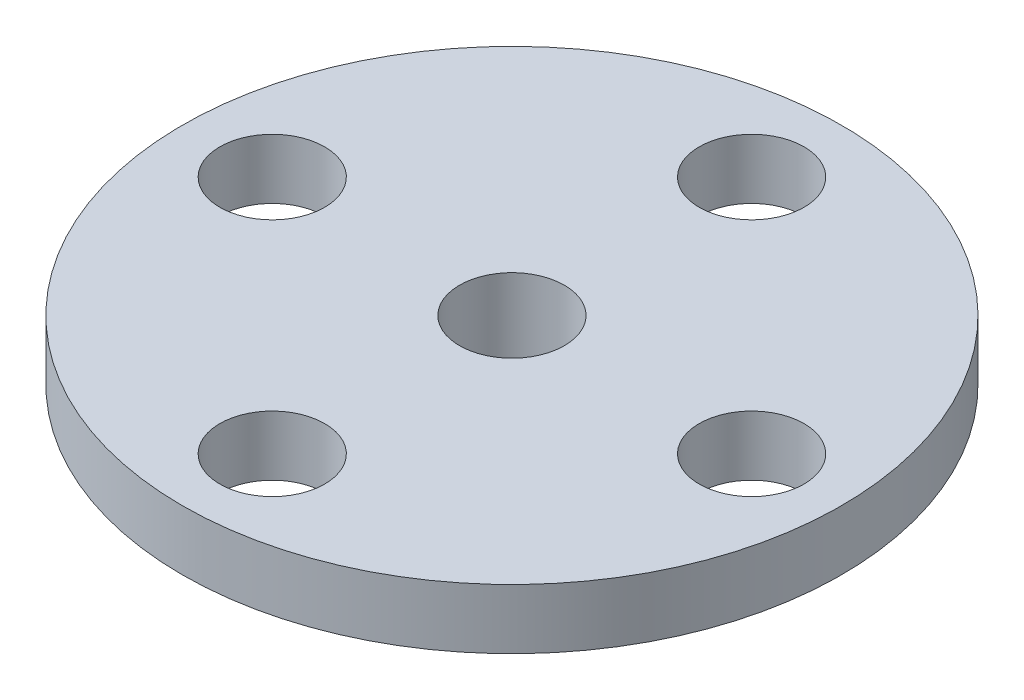
SolidWorks part; units mm, degrees
material "2024 Alloy"
ref_plane "Front Plane" through (0, 0, 0) normal (0, 0, 1) x (1, 0, 0)
ref_plane "Top Plane" through (0, 0, 0) normal (0, 1, 0) x (1, 0, 0)
ref_plane "Right Plane" through (0, 0, 0) normal (1, 0, 0) x (0, 0, -1)
ref_plane "Plane1" through (0, 0, 0) normal (0, 0, -1) x (-1, 0, 0)
sketch "Sketch1" plane through (0, 0, 0) normal (0, 0, -1) x (-1, 0, 0)
  line L0 (-11, 0) -> (0, 0)
  line L1 (0, 0) -> (0, 2)
  line L2 (0, 2) -> (-11, 2)
  line L3 (-11, 2) -> (-11, 0)
  line L4 (0, 0) -> (0, 2) construction
revolve "Revolve1" add sketch "Sketch1" angle 360 about L4
sketch "Sketch2" plane through (0, 0, 0) normal (0, -1, 0) x (1, 0, 0)
  circle A0 centre (0, 0) radius 4.4
extrude "Boss-Extrude1" add sketch "Sketch2" along normal blind 4.2
hole_wizard "Ø3.5 (3.5) Diameter Hole1" positions "Sketch4" profile "Sketch3" hole size "Ø3.5" standard "ANSI Metric"
sketch "Sketch4" plane through (0, 0, 0) normal (0, -1, 0) x (-1, 0, 0)
  point P0 (-8, 0)
  point P1 (0, -8)
  point P2 (8, 0)
  point P3 (0, 8)
sketch "Sketch3" plane through (8, 0, 0) normal (1, 0, 0) x (0, 0, -1)
  line L0 (0, 0) -> (0, 2)
  line L1 (0, 2) -> (1.75, 2)
  line L2 (1.75, 2) -> (1.75, 0)
  line L5 (1.75, 0) -> (0, 0)
  line L11 (0, -6.35) -> (0, 107.95) construction
  dimension "Thru Hole Dia." = 3.5
  dimension "Thru Hole Depth" = 2
hole_wizard "CBORE for M3 Hex Head Machine Screw1" positions "Sketch6" profile "Sketch5" counterbore size "M3" standard "ANSI Metric"
sketch "Sketch6" plane through (0, -4.2, 0) normal (0, -1, 0) x (-1, 0, 0)
  point P0 (0, 0)
sketch "Sketch5" plane through (0, -4.2, 0) normal (1, 0, 0) x (0, 0, -1)
  line L0 (0, 0) -> (0, 6.2)
  line L1 (0, 6.2) -> (1.75, 6.2)
  line L3 (1.75, 6.2) -> (1.75, 3)
  line L4 (1.75, 3) -> (2.85, 3)
  line L5 (2.85, 3) -> (2.85, 0)
  line L7 (2.85, 0) -> (0, 0)
  line L11 (0, -6.35) -> (0, 107.95) construction
  dimension "Thru Hole Dia." = 3.5
  dimension "Thru Hole Depth" = 6.2
  dimension "C'Bore Dia." = 5.7
  dimension "C'Bore Depth" = 3
